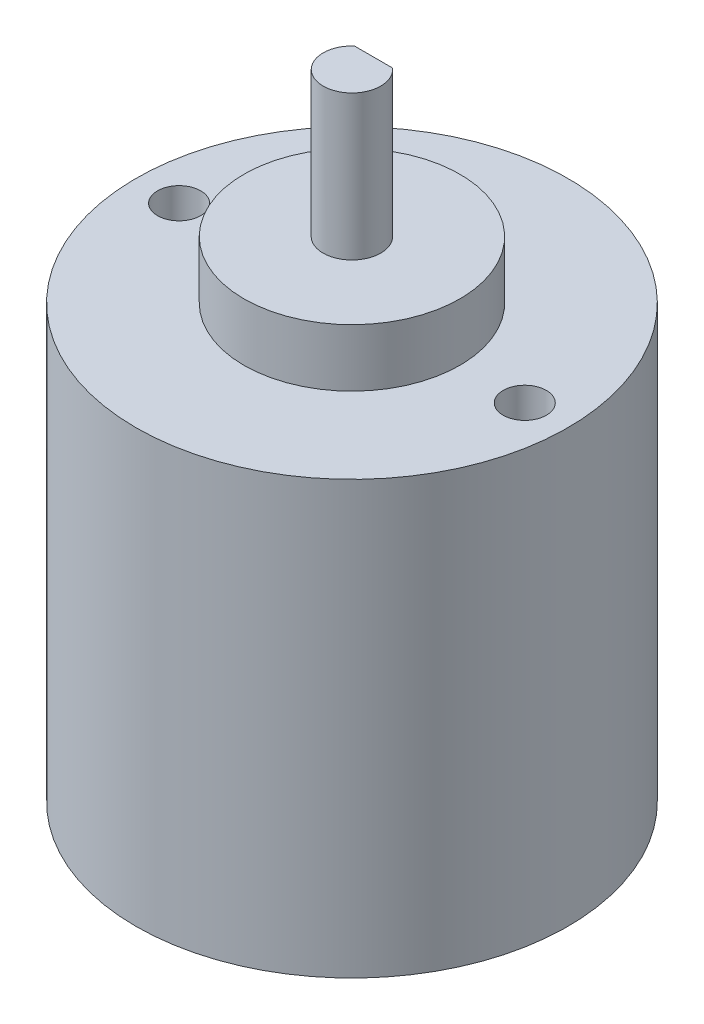
SolidWorks part; units mm, degrees
ref_plane "Front Plane" through (0, 0, 0) normal (0, 0, 1) x (1, 0, 0)
ref_plane "Top Plane" through (0, 0, 0) normal (0, 1, 0) x (1, 0, 0)
ref_plane "Right Plane" through (0, 0, 0) normal (1, 0, 0) x (0, 0, -1)
sketch "Sketch1" plane through (0, 0, 0) normal (0, 1, 0) x (1, 0, 0)
  circle A0 centre (0, 0) radius 15
  dimension "D1" = 30
extrude "Boss-Extrude1" add sketch "Sketch1" along normal blind 30 contours A0
sketch "Sketch4" plane through (0, 30, 0) normal (0, 1, 0) x (1, 0, 0)
  line L0 (-12.005, 0) -> (12.005, 0) construction
  circle A0 centre (0, 0) radius 12.005 construction
  circle A1 centre (12.005, 0) radius 1.5
  circle A2 centre (-12.005, 0) radius 1.5
  dimension "D1" = 24.01
  dimension "D2" = 3
extrude "Cut-Extrude1" cut sketch "Sketch4" against normal blind 4
sketch "Sketch5" plane through (0, 30, 0) normal (0, 1, 0) x (1, 0, 0)
  circle A0 centre (0, 0) radius 7.5
  dimension "D1" = 15
extrude "Boss-Extrude2" add sketch "Sketch5" along normal blind 4
sketch "Sketch6" plane through (0, 34, 0) normal (0, 1, 0) x (1, 0, 0)
  circle A0 centre (0, 0) radius 2
  dimension "D1" = 4
extrude "Boss-Extrude3" add sketch "Sketch6" along normal blind 2.05
sketch "Sketch7" plane through (0, 36.05, 0) normal (0, 1, 0) x (1, 0, 0)
  line L0 (0, -2) -> (0, 1.5) construction
  line L1 (-1.3229, 1.5) -> (1.3229, 1.5)
  circle A0 centre (0, 0) radius 2 construction
  circle A1 centre (0, 0) radius 2 construction
  arc A2 (-1.3229, 1.5) -> (1.3229, 1.5) centre (0, 0) ccw
  dimension "D1" = 3.5
extrude "Boss-Extrude4" add sketch "Sketch7" along normal blind 8
sketch "Sketch9" plane through (0, 0, 0) normal (0, -1, 0) x (1, 0, 0)
  line L0 (0, 0) -> (0, -8) construction
  circle A0 centre (0, -8) radius 5
  dimension "D2" = 10
  dimension "D1" = 8
extrude "Boss-Extrude5" add sketch "Sketch9" along normal blind 2.5
